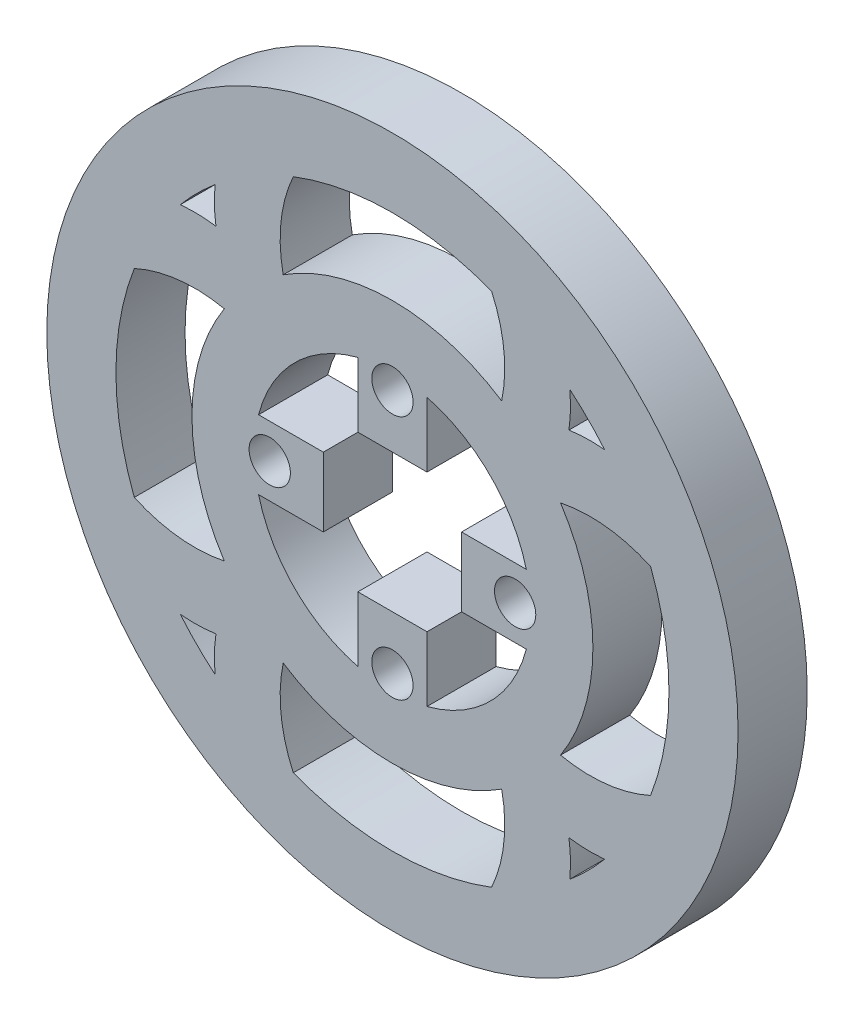
SolidWorks part; units mm, degrees
ref_plane "Front Plane" through (0, 0, 0) normal (0, 0, 1) x (1, 0, 0)
ref_plane "Top Plane" through (0, 0, 0) normal (0, 1, 0) x (1, 0, 0)
ref_plane "Right Plane" through (0, 0, 0) normal (1, 0, 0) x (0, 0, -1)
sketch "Sketch6" plane through (0, 0, 0) normal (0, 0, 1) x (1, 0, 0)
  circle A0 centre (0, 0) radius 20
  circle A1 centre (0, 0) radius 29
  dimension "D1" = 40
  dimension "D2" = 58
extrude "Inner Ring" add sketch "Sketch6" against normal blind 10 separate body
sketch "Sketch7" plane through (0, 0, 0) normal (0, 0, 1) x (1, 0, 0)
  line L2 (-10, 5) -> (-10, -5)
  line L3 (-5, 10) -> (5, 10)
  line L4 (10, 5) -> (10, -5)
  line L5 (-5, -10) -> (5, -10)
  line L14 (-19.3649, 5) -> (-10, 5)
  line L15 (-19.3649, -5) -> (-10, -5)
  line L16 (-5, 19.3649) -> (-5, 10)
  line L17 (5, 19.3649) -> (5, 10)
  line L18 (19.3649, 5) -> (10, 5)
  line L19 (19.3649, -5) -> (10, -5)
  line L20 (5, -19.3649) -> (5, -10)
  line L21 (-5, -19.3649) -> (-5, -10)
  circle A1 centre (0, 0) radius 20
  circle M19 centre (0, 0) radius 20
  dimension "D1" = 20
  dimension "D2" = 20
  dimension "D3" = 10
  dimension "D5" = 10
  dimension "D7" = 10
  dimension "D8" = 10
extrude "Motor Connector Cut" add sketch "Sketch7" against normal blind 10 contours L19 L18 L4 M19 | L17 L16 L3 M19 | L15 L2 L14 M19 | L21 L20 L5 M19
sketch "Sketch8" plane through (0, 0, 0) normal (0, 0, 1) x (1, 0, 0)
  circle A1 centre (0, 17.75) radius 2.987
  circle A2 centre (17.75, 0) radius 2.987
  circle A3 centre (0, -17.75) radius 2.987
  circle A4 centre (-17.75, 0) radius 2.987
  dimension "D1" = 5.974
  dimension "D2" = 5.974
  dimension "D3" = 5.974
  dimension "0.0049m" = 5.974
sketch "Sketch9" plane through (0, 0, 0) normal (0, 0, 1) x (1, 0, 0)
  circle A0 centre (0, 0) radius 50
  circle A18 centre (0, 0) radius 29
  dimension "D2" = 100
extrude "Outside Ring Extrusion" add sketch "Sketch9" against normal blind 10
sketch "Sketch12" plane through (0, 0, 0) normal (0, 0, 1) x (1, 0, 0)
  circle A0 centre (0, 0) radius 27.5
  circle A1 centre (0, 0) radius 45
  dimension "D1" = 55
  dimension "D2" = 90
extrude "Cut-Extrude6" cut sketch "Sketch12" against normal blind 55
extrude "Motor Connector Holes" cut sketch "Sketch8" against normal blind 10
sketch "Sketch10" plane through (0, 0, 0) normal (0, 0, 1) x (1, 0, 0)
  circle A0 centre (0, 0) radius 29
  arc A4 (-24.0947, 20.4191) -> (-41.6064, 16.7952) centre (-29, 0) ccw
  circle A5 centre (0, 0) radius 50
  arc A6 (-0.0957, 0) -> (0, 0.0957) centre (-17.7016, 17.7016) ccw
  arc A9 (-28.6072, 4.7568) -> (-42.4805, -14.6492) centre (-17.7016, -17.7016) ccw
  arc A10 (-20.4191, 24.0947) -> (-38.2638, 23.4049) centre (-28.6072, 4.7568) ccw
  arc A11 (-24.3176, 15.8004) -> (-43.8179, 9.722) centre (-28.6072, -4.7568) ccw
  circle A18 centre (0, 0) radius 29
  arc A19 (14.3758, 42.4453) -> (-4.7568, 28.6072) centre (17.7016, 17.7016) ccw
  circle A20 centre (0, -0.0957) radius 44.9043
  arc A21 (24.3176, -15.8004) -> (43.8731, -9.6638) centre (28.6072, 4.7568) ccw
  arc A22 (43.8179, 9.722) -> (24.3176, 15.8004) centre (28.6072, -4.7568) ccw
  arc A23 (41.6064, 16.7952) -> (21.3966, 19.5752) centre (29, 0) ccw
  arc A24 (49.5968, 4.0954) -> (49.3228, 8.2014) centre (28.6072, 4.7568) ccw
  arc A25 (49.5968, -4.0954) -> (49.5968, 4.0954) centre (29, 0) ccw
  arc A26 (28.6072, -4.7568) -> (42.4628, 14.5092) centre (17.7016, 17.7016) ccw
  arc A27 (42.4805, -14.6492) -> (28.6072, 4.7568) centre (17.7016, -17.7016) ccw
  arc A28 (49.3228, -8.2014) -> (49.5968, -4.0954) centre (28.6072, -4.7568) ccw
  arc A29 (25.5301, 25.5301) -> (23.4328, 38.2096) centre (4.7568, 28.6072) ccw
  arc A30 (23.2856, -38.4907) -> (22.8197, -17.8959) centre (4.7568, -28.6072) ccw
  arc A31 (20.4191, 24.0947) -> (16.8561, 41.5248) centre (0, 29) ccw
  arc A32 (24.0947, -20.4191) -> (41.717, -16.7116) centre (29, 0) ccw
  arc A33 (15.8004, 24.3176) -> (9.8231, 43.721) centre (-4.7568, 28.6072) ccw
  arc A34 (4.7568, 28.6072) -> (-14.3758, 42.4453) centre (-17.7016, 17.7016) ccw
  arc A35 (16.6483, -41.7998) -> (20.4191, -24.0947) centre (0, -29) ccw
  arc A36 (9.5599, -43.9706) -> (15.8004, -24.3176) centre (-4.7568, -28.6072) ccw
  arc A38 (17.8959, -22.8197) -> (38.435, -23.3152) centre (28.6072, -4.7568) ccw
  arc A39 (-14.7836, -42.4967) -> (4.7568, -28.6072) centre (-17.7016, -17.7016) ccw
  arc A40 (-38.435, -23.3152) -> (-20.4191, -24.0947) centre (-28.6072, -4.7568) ccw
  arc A41 (-43.8731, -9.6638) -> (-24.3176, -15.8004) centre (-28.6072, 4.7568) ccw
  arc A43 (-41.717, -16.7116) -> (-21.3966, -19.5752) centre (-29, 0) ccw
  arc A44 (0, -0.0957) -> (-0.0957, 0) centre (-17.7016, -17.7016) ccw
  arc A45 (-42.4628, 14.5092) -> (-28.6072, -4.7568) centre (-17.7016, 17.7016) ccw
  arc A46 (-4.7568, -28.6072) -> (14.7836, -42.4967) centre (17.7016, -17.7016) ccw
  arc A47 (-23.4328, 38.2096) -> (-24.0947, 20.4191) centre (-4.7568, 28.6072) ccw
  arc A48 (-15.8004, -24.3176) -> (-9.5599, -43.9706) centre (4.7568, -28.6072) ccw
  arc A49 (-16.8561, 41.5248) -> (-19.5752, 21.3966) centre (0, 29) ccw
  arc A50 (-20.4191, -24.0947) -> (-16.6483, -41.7998) centre (0, -29) ccw
  arc A51 (-9.8231, 43.721) -> (-15.8004, 24.3176) centre (4.7568, 28.6072) ccw
  arc A52 (-25.5301, -25.5301) -> (-23.2856, -38.4907) centre (-4.7568, -28.6072) ccw
  arc A53 (4.0954, 49.5968) -> (-4.0954, 49.5968) centre (0, 29) ccw
  arc A54 (8.2014, 49.3228) -> (0, 49.0614) centre (4.7568, 28.6072) ccw
  arc A55 (0, 49.0614) -> (-8.2014, 49.3228) centre (-4.7568, 28.6072) ccw
  arc A56 (38.2638, 23.4049) -> (25.5301, 25.5301) centre (28.6072, 4.7568) ccw
  circle A57 centre (-0.0957, 0) radius 27.4043
extrude "Pattern" add sketch "Sketch10" against normal blind 10
sketch "Sketch13" plane through (0, 0, -10) normal (0, 0, -1) x (-1, 0, 0)
  circle A0 centre (0, 0) radius 45
  circle A1 centre (0, 0) radius 40
  dimension "D1" = 90
  dimension "D2" = 80
extrude "Boss-Extrude1" add sketch "Sketch13" against normal blind 10
